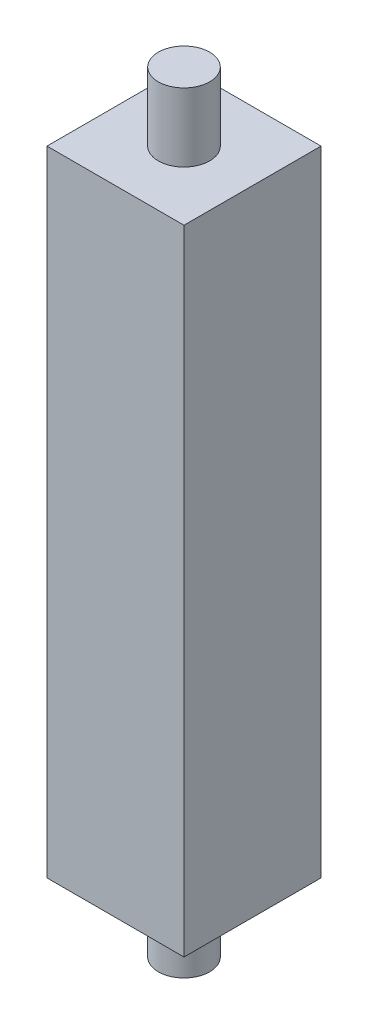
SolidWorks part; units mm, degrees
ref_plane "Front Plane" through (0, 0, 0) normal (0, 0, 1) x (1, 0, 0)
ref_plane "Top Plane" through (0, 0, 0) normal (0, 1, 0) x (1, 0, 0)
ref_plane "Right Plane" through (0, 0, 0) normal (1, 0, 0) x (0, 0, -1)
sketch "Sketch1" plane through (0, 0, 0) normal (0, 1, 0) x (1, 0, 0)
  line L1 (-20, 20) -> (20, 20)
  line L2 (-20, 20) -> (-20, -20)
  line L3 (-20, -20) -> (20, -20)
  line L4 (20, 20) -> (20, -20)
  line L5 (-20, 20) -> (20, -20) construction
  line L6 (-20, -20) -> (20, 20) construction
  point P1 (0, 0)
  dimension "D1" = 40
  dimension "D2" = 40
extrude "Boss-Extrude1" add sketch "Sketch1" along normal blind 185
sketch "Sketch2" plane through (0, 185, 0) normal (0, 1, 0) x (1, 0, 0)
  circle A0 centre (0, 0) radius 7.5
  dimension "D1" = 15
extrude "Boss-Extrude2" add sketch "Sketch2" along normal blind 20 and the other way blind 205
